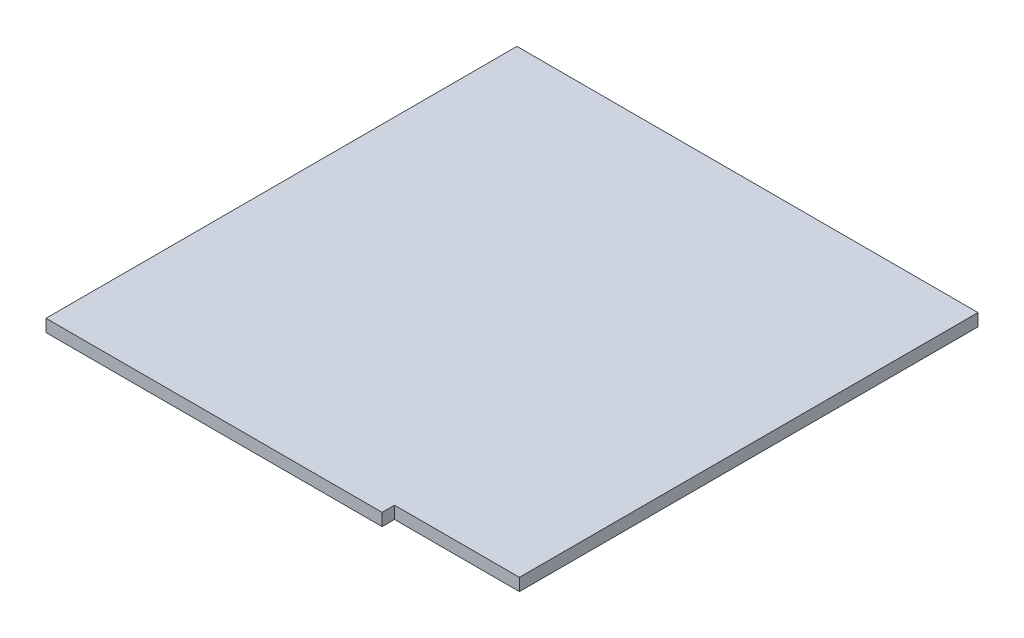
SolidWorks part; units mm, degrees
ref_plane "Front Plane" through (0, 0, 0) normal (0, 0, 1) x (1, 0, 0)
ref_plane "Top Plane" through (0, 0, 0) normal (0, 1, 0) x (1, 0, 0)
ref_plane "Right Plane" through (0, 0, 0) normal (1, 0, 0) x (0, 0, -1)
sketch "Sketch1" plane through (0, 0, 0) normal (0, 1, 0) x (1, 0, 0)
  line L0 (430.53, 0) -> (430.53, 15.875)
  line L1 (0, 0) -> (430.53, 0)
  line L2 (0, 0) -> (0, 603.25)
  line L3 (0, 603.25) -> (590.55, 603.25)
  line L4 (590.55, 15.875) -> (590.55, 603.25)
  line L5 (430.53, 15.875) -> (590.55, 15.875)
  line L7 (0, 15.875) -> (590.55, 15.875) construction
  line L8 (430.53, 0) -> (430.53, 603.25) construction
  line L9 (0, 0) -> (590.55, 0) construction
  line L10 (590.55, 0) -> (590.55, 603.25) construction
  dimension "D1" = 603.25
  dimension "D3" = 160.02
  dimension "D4" = 15.875
extrude "Boss-Extrude1" add sketch "Sketch1" along normal blind 15.875
